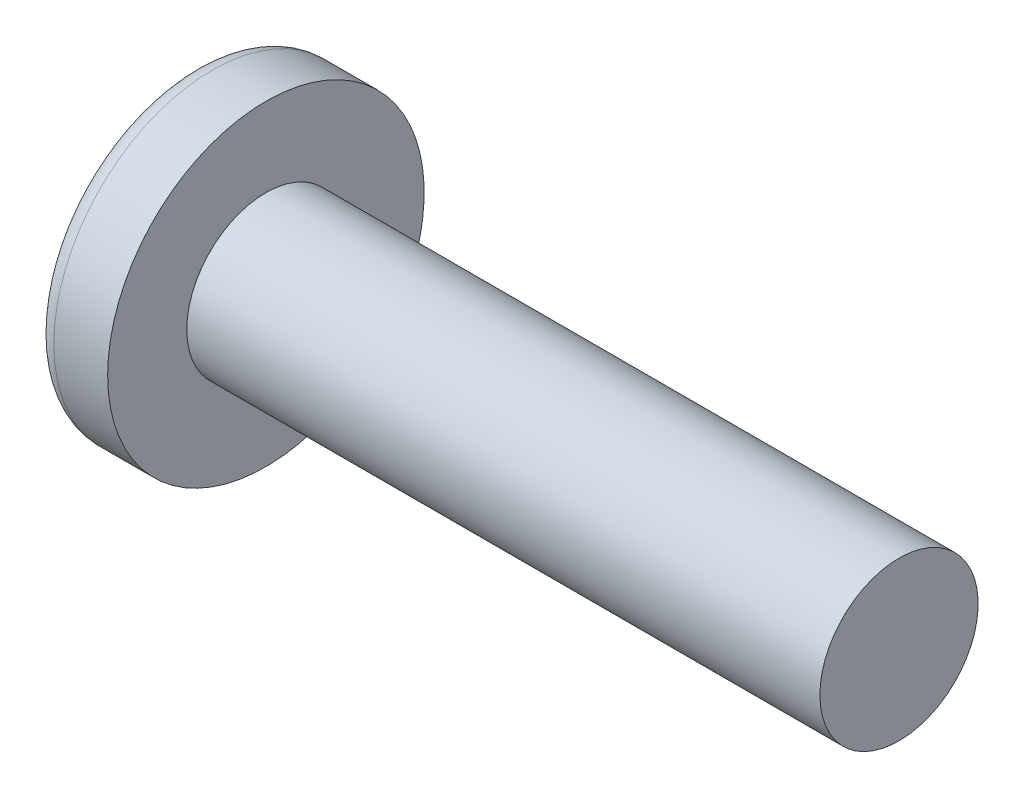
SolidWorks part; units mm, degrees
ref_plane "Plane1" through (0, 0, 0) normal (0, 0, 1) x (1, 0, 0)
ref_plane "Plane2" through (0, 0, 0) normal (0, 1, 0) x (1, 0, 0)
ref_plane "Plane3" through (0, 0, 0) normal (1, 0, 0) x (0, 0, -1)
other "Configuration Table"
sketch "BodySke" plane through (0, 0, 0) normal (0, 0, 1) x (1, 0, 0)
  line L0 (7.5, 5) -> (7.5, 10)
  line L1 (9, 6.35) -> (9, -3.175) construction
  line L2 (-25.4, 0) -> (127, 0) construction
  line L3 (47.5, 0) -> (0, 0)
  line L4 (7.5, 5) -> (47.5, 5)
  line L5 (47.5, 5) -> (47.5, 0)
  line L6 (4.1004, 10) -> (7.5, 10)
  line L7 (7.5, -5) -> (47.5, -5) construction
  line L8 (7.5, 6.35) -> (7.5, -3.175) construction
  arc A0 (3.1356, 9.5135) -> (0, 0) centre (16, 0) ccw
  arc A2 (3.1356, 9.5135) -> (4.1004, 10) centre (4.1004, 8.8) cw
revolve "Base-Revolve" add sketch "BodySke" angle 360 about L2
cosmetic thread "ThreadCosmetic" [suppressed] parameters "Thread_length"=24.6, "Thread_minor"=8.344
sketch "Sketch3" plane through (0, 0, 0) normal (1, 0, 0) x (0, 0, -1)
  line L0 (0.92, -5.09) -> (-0.92, -5.09)
  line L1 (0.92, -5.09) -> (0.92, 5.09)
  line L2 (-0.92, 5.09) -> (0.92, 5.09)
  line L3 (-0.92, 5.09) -> (-0.92, -5.09)
  dimension "D1" = 0.91
  dimension "D2" = 0.24
ref_plane "Plane4" through (6.09, 0, 0) normal (1, 0, 0) x (0, 0, -1)
sketch "Sketch4" plane through (6.09, 0, 0) normal (1, 0, 0) x (0, 0, -1)
  line L0 (0.46, -0.46) -> (-0.46, -0.46)
  line L1 (0.46, -0.46) -> (0.46, 0.46)
  line L2 (-0.46, 0.46) -> (0.46, 0.46)
  line L3 (-0.46, 0.46) -> (-0.46, -0.46)
  dimension "D2" = 0.24
  dimension "D1" = 0.24
  dimension "D3" = 0.12
  dimension "D4" = 0.12
loft "Cut-Loft1" cut profiles "Sketch3", "Sketch4"
pattern_circular "CirPattern1" count 2 every 90 about axis through (0, 0, 0) along (1, 0, 0) of "Cut-Loft1"
sketch "ThdSchSke" plane through (0, 0, 0) normal (0, 0, 1) x (1, 0, 0)
  line L0 (9, -4.172) -> (8.4202, -5)
  line L1 (9, -4.172) -> (9.5798, -5)
  line L2 (9.5798, -5) -> (9.5798, -6.25)
  line L3 (-3.175, 0) -> (5.1513, 0) construction
  line L5 (9.5798, -6.25) -> (8.4202, -6.25)
  line L6 (8.4202, -6.25) -> (8.4202, -5)
  dimension "SideAngle" = 55
  dimension "VeeAngle" = 70
  dimension "Thread_minor" = 1.548
  dimension "Overcut" = 2.5
  dimension "Diameter" = 2
  dimension "Start" = 2
revolve "ThreadSchematic" [suppressed] cut sketch "ThdSchSke" angle 360 about L3
pattern_linear "ThdSchPat" [suppressed]
equation "\"D1@Sketch3\" = \"Cross_dia@Sketch3\" / 2"
equation "\"D2@Sketch3\" = \"Cross_width@Sketch3\" / 2"
equation "\"D1@Sketch4\" = \"Cross_width@Sketch3\" *.5"
equation "\"D2@Sketch4\" = \"D1@Sketch4\""
equation "\"D3@Sketch4\" = \"D1@Sketch4\" / 2"
equation "\"D4@Sketch4\" = \"D2@Sketch4\" / 2"
equation "\"Thread_length@ThreadCosmetic\" = ((sgn( (\"Length@BodySke\" - \"Advance@BodySke\" ) - \"Thread_nom@BodySke\" )-1)*( (\"Length@BodySke\" - \"Advance@BodySke\" ) - \"Thread_nom@BodySke\" ))/-2+ \"Thread_nom@BodySke\""
equation "\"Thread_minor@ThdSchSke\" = \"Thread_minor@ThreadCosmetic\""
equation "\"Diameter@ThdSchSke\" = \"Diameter@BodySke\""
equation "\"Overcut@ThdSchSke\" = \"Diameter@BodySke\" * 1.25"
equation "\"Start@ThdSchSke\" = \"Head_ht@BodySke\" + \"Length@BodySke\" - \"Thread_length@ThreadCosmetic\"  '---Non-countersunk---"
equation "\"Num_threads@ThdSchPat\" = int( \"Thread_length@ThreadCosmetic\" / \"Advance@BodySke\" + 0.999 )  + 1"
equation "\"Advance@ThdSchPat\" = \"Thread_length@ThreadCosmetic\" /  (\"Num_threads@ThdSchPat\" - 1) 'relax it"
